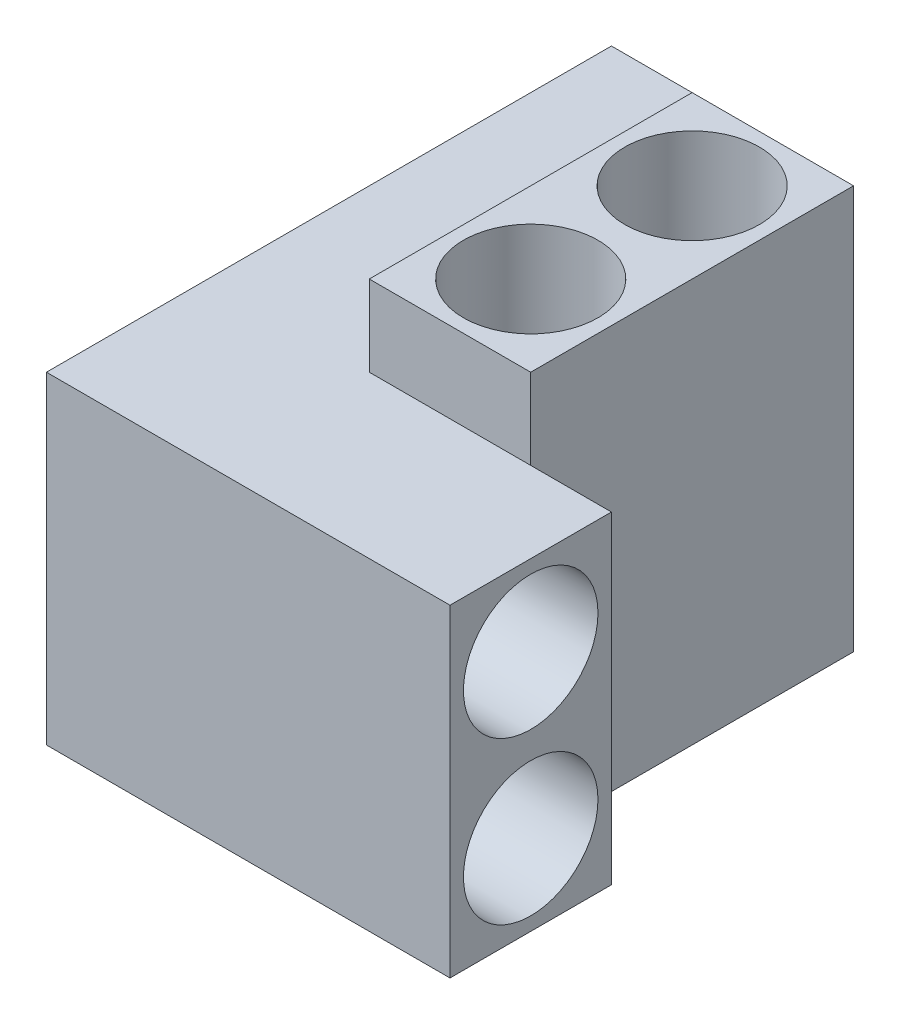
SolidWorks part; units mm, degrees
ref_plane "Front Plane" through (0, 0, 0) normal (0, 0, 1) x (1, 0, 0)
ref_plane "Top Plane" through (0, 0, 0) normal (0, 1, 0) x (1, 0, 0)
ref_plane "Right Plane" through (0, 0, 0) normal (1, 0, 0) x (0, 0, -1)
sketch "Sketch1" plane through (0, 0, 0) normal (0, 1, 0) x (1, 0, 0)
  line L1 (0, 0) -> (15.875, 0)
  line L2 (0, 0) -> (0, 6.35)
  line L3 (0, 6.35) -> (15.875, 6.35)
  line L4 (15.875, 0) -> (15.875, 6.35)
  line L5 (0, 6.35) -> (6.35, 6.35)
  line L6 (0, 6.35) -> (0, 22.225)
  line L7 (0, 22.225) -> (6.35, 22.225)
  line L8 (6.35, 6.35) -> (6.35, 22.225)
  dimension "D1" = 15.875
  dimension "D2" = 6.35
extrude "Boss-Extrude1" add sketch "Sketch1" along normal blind 6.35 contours L3 L8 L7 L6 | L1 L4 L3 L2
sketch "Sketch5" plane through (15.875, 0, 0) normal (1, 0, 0) x (0, 0, -1)
  line L0 (6.35, 6.35) -> (6.35, 0) construction
  line L1 (0, 6.35) -> (6.35, 6.35) construction
  circle A0 centre (3.175, 3.175) radius 2.6458
  dimension "D1" = 5.2917
  dimension "D2" = 3.175
  dimension "D3" = 3.175
extrude "Cut-Extrude1" cut sketch "Sketch5" against normal blind 12.7
sketch "Sketch6" plane through (0, 0, -22.225) normal (0, 0, -1) x (-1, 0, 0)
  line L0 (0, 6.35) -> (0, 0) construction
  line L1 (0, 6.35) -> (-6.35, 6.35) construction
  circle A0 centre (-3.175, 3.175) radius 2.6458
  dimension "D1" = 5.2917
  dimension "D2" = 3.175
  dimension "D3" = 3.175
extrude "Cut-Extrude2" cut sketch "Sketch6" against normal blind 12.7
sketch "Sketch10" plane through (0, 6.35, 0) normal (0, 1, 0) x (1, 0, 0)
  line L1 (0, 0) -> (15.875, 0)
  line L2 (0, 0) -> (0, 6.35)
  line L3 (0, 6.35) -> (15.875, 6.35)
  line L4 (15.875, 0) -> (15.875, 6.35)
  line L5 (6.35, 22.225) -> (0, 22.225)
  line L6 (6.35, 22.225) -> (6.35, 6.35)
  line L7 (6.35, 6.35) -> (0, 6.35)
  line L8 (0, 22.225) -> (0, 6.35)
  line M1 (0, 22.225) -> (0, 0)
  line M2 (0, 0) -> (15.875, 0)
  line M3 (15.875, 0) -> (15.875, 6.35)
  line M4 (15.875, 6.35) -> (6.35, 6.35)
  line M5 (6.35, 6.35) -> (6.35, 22.225)
  line M6 (6.35, 22.225) -> (0, 22.225)
extrude "Boss-Extrude5" add sketch "Sketch10" along normal blind 6.35 contours L3 M1 M5 M6 | L3 M1 M2 M3 M4
sketch "Sketch11" plane through (15.875, 0, 0) normal (1, 0, 0) x (0, 0, -1)
  line L0 (0, 12.7) -> (0, 0) construction
  line L1 (0, 12.7) -> (6.35, 12.7) construction
  circle A0 centre (3.175, 9.525) radius 2.6458
  dimension "D3" = 5.2917
  dimension "D1" = 3.175
  dimension "D2" = 3.175
extrude "Cut-Extrude5" cut sketch "Sketch11" against normal blind 12.7
sketch "Sketch12" plane through (0, 0, -22.225) normal (0, 0, -1) x (-1, 0, 0)
  line L0 (0, 12.7) -> (0, 0) construction
  line L1 (-6.35, 12.7) -> (0, 12.7) construction
  circle A0 centre (-3.175, 9.525) radius 2.6458
  dimension "D1" = 5.2917
  dimension "D2" = 3.175
  dimension "D3" = 3.175
extrude "Cut-Extrude6" cut sketch "Sketch12" against normal blind 12.7
sketch "Sketch13" plane through (0, 12.7, 0) normal (0, 1, 0) x (1, 0, 0)
  line L1 (6.35, 6.35) -> (12.7, 6.35)
  line L2 (6.35, 6.35) -> (6.35, 19.05)
  line L3 (6.35, 19.05) -> (12.7, 19.05)
  line L4 (12.7, 6.35) -> (12.7, 19.05)
  dimension "D1" = 12.7
  dimension "D2" = 6.35
extrude "Boss-Extrude6" add sketch "Sketch13" along normal blind 3.175 and the other way blind 12.7
sketch "Sketch14" plane through (0, 15.875, 0) normal (0, 1, 0) x (1, 0, 0)
  line L0 (12.7, 6.35) -> (12.7, 19.05) construction
  line L1 (12.7, 19.05) -> (6.35, 19.05) construction
  line L2 (6.35, 6.35) -> (12.7, 6.35) construction
  circle A0 centre (9.525, 9.525) radius 2.6458
  circle A1 centre (9.525, 15.875) radius 2.6458
  dimension "D3" = 5.2917
  dimension "D6" = 5.2917
  dimension "D1" = 3.175
  dimension "D2" = 3.175
  dimension "D4" = 3.175
  dimension "D5" = 3.175
extrude "Cut-Extrude7" cut sketch "Sketch14" against normal blind 12.7
